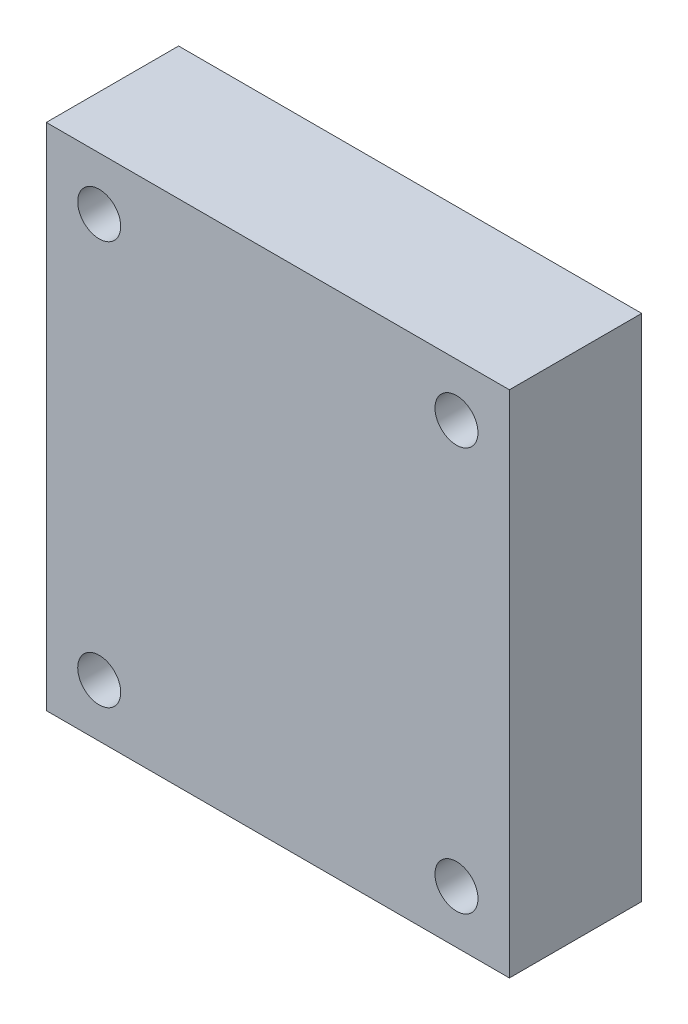
SolidWorks part; units mm, degrees
material "Plain Carbon Steel"
ref_plane "Front Plane" through (0, 0, 0) normal (0, 0, 1) x (1, 0, 0)
ref_plane "Top Plane" through (0, 0, 0) normal (0, 1, 0) x (1, 0, 0)
ref_plane "Right Plane" through (0, 0, 0) normal (1, 0, 0) x (0, 0, -1)
sketch "Sketch1" plane through (0, 0, 0) normal (0, 0, 1) x (1, 0, 0)
  line L0 (-70, -77) -> (70, -77)
  line L1 (-70, -77) -> (-70, 77)
  line L2 (70, -77) -> (70, 77)
  line L3 (-70, 77) -> (70, 77)
  line L4 (-70, -77) -> (70, 77) construction
  line L5 (70, -77) -> (-70, 77) construction
  line L6 (-70, 0) -> (70, 0) construction
  line L7 (0, 77) -> (0, -77) construction
  circle A0 centre (-54, 61) radius 6.5
  circle A1 centre (54, 61) radius 6.5
  circle A2 centre (54, -61) radius 6.5
  circle A3 centre (-54, -61) radius 6.5
  point P1 (0, 0)
  dimension "D3" = 13
  dimension "D5" = 16
  dimension "D1" = 140
  dimension "D2" = 16
  dimension "D4" = 154
extrude "Boss-Extrude1" add sketch "Sketch1" along normal mid plane 40
